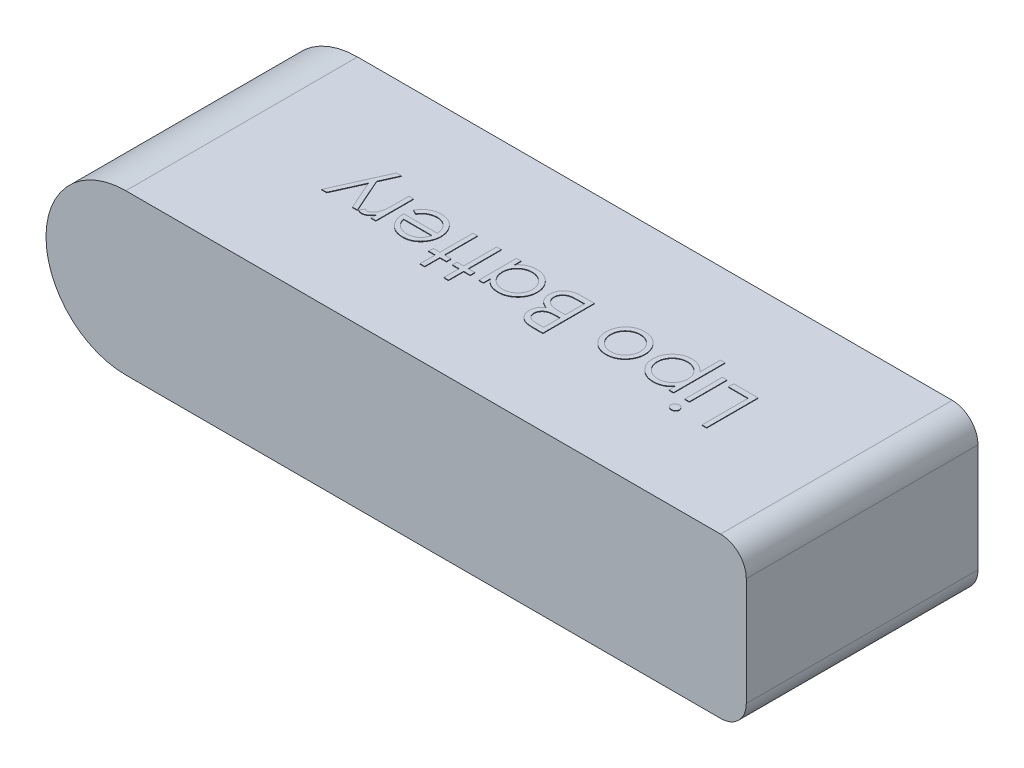
SolidWorks part; units mm, degrees
ref_plane "Front Plane" through (0, 0, 0) normal (0, 0, 1) x (1, 0, 0)
ref_plane "Top Plane" through (0, 0, 0) normal (0, 1, 0) x (1, 0, 0)
ref_plane "Right Plane" through (0, 0, 0) normal (1, 0, 0) x (0, 0, -1)
sketch "Sketch1" plane through (0, 0, 0) normal (0, 0, 1) x (1, 0, 0)
  line L0 (0, 0) -> (105, 0) construction
  line L1 (0, 15.5) -> (105, 15.5)
  line L2 (0, -15.5) -> (105, -15.5)
  line L4 (105, -15.5) -> (120.5, -15.5)
  line L5 (105, -15.5) -> (105, 15.5)
  line L6 (105, 15.5) -> (120.5, 15.5)
  line L7 (120.5, -15.5) -> (120.5, 15.5)
  arc A0 (0, 15.5) -> (0, -15.5) centre (0, 0) ccw
  arc A1 (105, -15.5) -> (105, 15.5) centre (105, 0) ccw
  point P3 (52.5, 0)
  dimension "D1" = 15.5
  dimension "D2" = 105
extrude "Boss-Extrude1" add sketch "Sketch1" along normal blind 45
fillet "Fillet1" radius 5 2 edges at (120.5, -15.5, 22.5) (120.5, 15.5, 22.5)
sketch "Sketch2" plane through (0, 15.5, 0) normal (0, 1, 0) x (-1, 0, 0)
  text T0 "Lipo Battery" font "Century Gothic" height 10
extrude "Boss-Extrude2" add sketch "Sketch2" along normal blind 0.1
